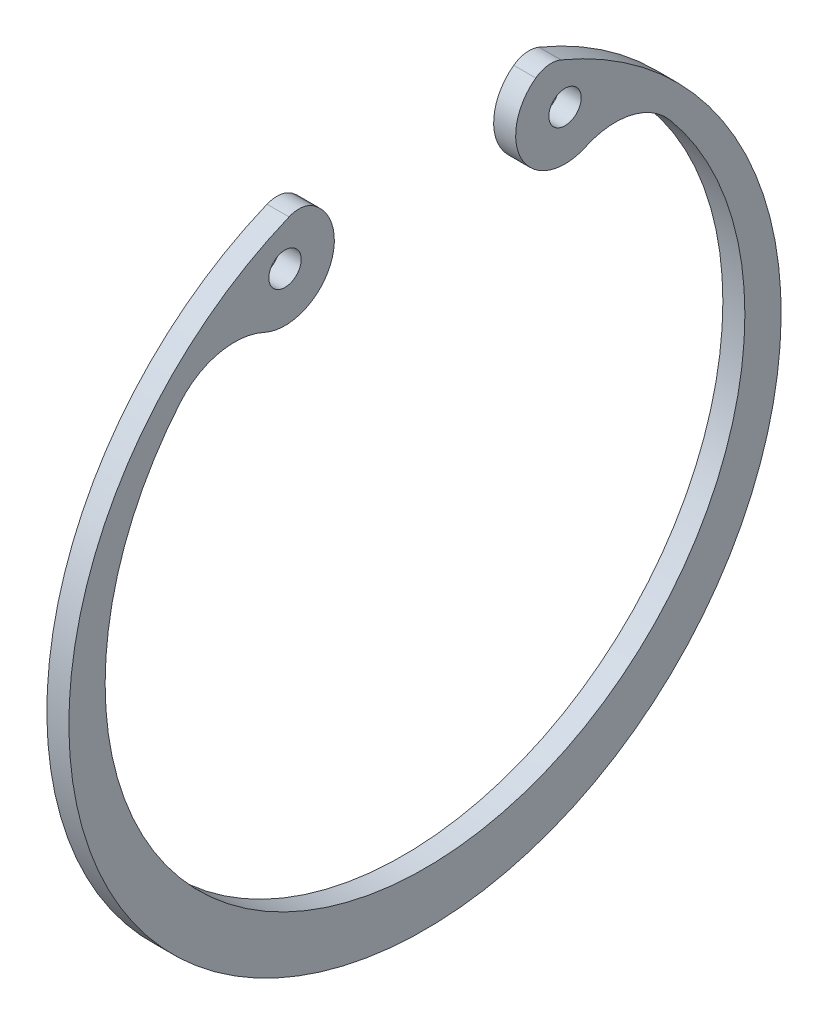
SolidWorks part; units mm, degrees
material "AISI Тип A2 Инструментальная сталь"
ref_plane "Спереди" through (0, 0, 0) normal (0, 0, 1) x (1, 0, 0)
ref_plane "Сверху" through (0, 0, 0) normal (0, 1, 0) x (1, 0, 0)
ref_plane "Справа" through (0, 0, 0) normal (1, 0, 0) x (0, 0, -1)
sketch "Эскиз1" plane through (0, 0, 0) normal (1, 0, 0) x (0, 0, -1)
  line L0 (0, -1000.3492) -> (0, 48999.6508) construction
  line L1 (8.5517, 25.1783) -> (12.4031, 18.6469) construction
  arc A10 (-10.501, 25.4161) -> (10.501, 25.4161) centre (0, 0) ccw
  circle A12 centre (10.8109, 22.1093) radius 1.25
  arc A13 (8.5517, 25.1783) -> (12.4031, 18.6469) centre (10.8109, 22.1093) ccw
  arc A14 (18.9122, 17.1877) -> (12.4031, 18.6469) centre (14.701, 13.65) ccw
  circle A15 centre (-10.8109, 22.1093) radius 1.25
  arc A16 (-18.9122, 17.1877) -> (-12.4031, 18.6469) centre (-14.701, 13.65) cw
  arc A17 (-8.5517, 25.1783) -> (-12.4031, 18.6469) centre (-10.8109, 22.1093) cw
  arc A18 (-8.5517, 25.1783) -> (-10.501, 25.4161) centre (-9.7373, 23.5677) ccw
  arc A19 (-18.9122, 17.1877) -> (18.9122, 17.1877) centre (0, 1.3) ccw
  arc A20 (8.5517, 25.1783) -> (10.501, 25.4161) centre (9.7373, 23.5677) cw
  point P21 (-9.6676, 25.7447)
  point P25 (9.6676, 25.7447)
  dimension "D1" = 55
  dimension "d4" = 2.5
  dimension "r1" = 5.5
  dimension "r2" = 2
  dimension "r2_2" = 2
  dimension "D2" = 24.7
  dimension "e" = 1.3
  dimension "a" = 6.7
  dimension "l" = 14
extrude "Бобышка-Вытянуть1" add sketch "Эскиз1" along normal blind 1.7
sketch "Эскиз канавки" plane through (0, 0, 0) normal (0, 0, 1) x (1, 0, 0)
  line L1 (1.7, -27.5) -> (-0.2, -27.5)
  line L2 (1.7, -27.5) -> (1.7, 0)
  line L3 (1.7, 0) -> (-0.2, 0)
  line L4 (-0.2, -27.5) -> (-0.2, 0)
  dimension "m" = 1.9
sketch "при одностор ось нагр" plane through (0, 0, 0) normal (0, 0, 1) x (1, 0, 0)
  line L0 (1.7, -27.5) -> (6.2, -27.5)
  dimension "h" = 4.5
equation "\"r2_2@Эскиз1\"=\"r2@Эскиз1\""
equation "\"D2@Эскиз1\"=49.4/2"
